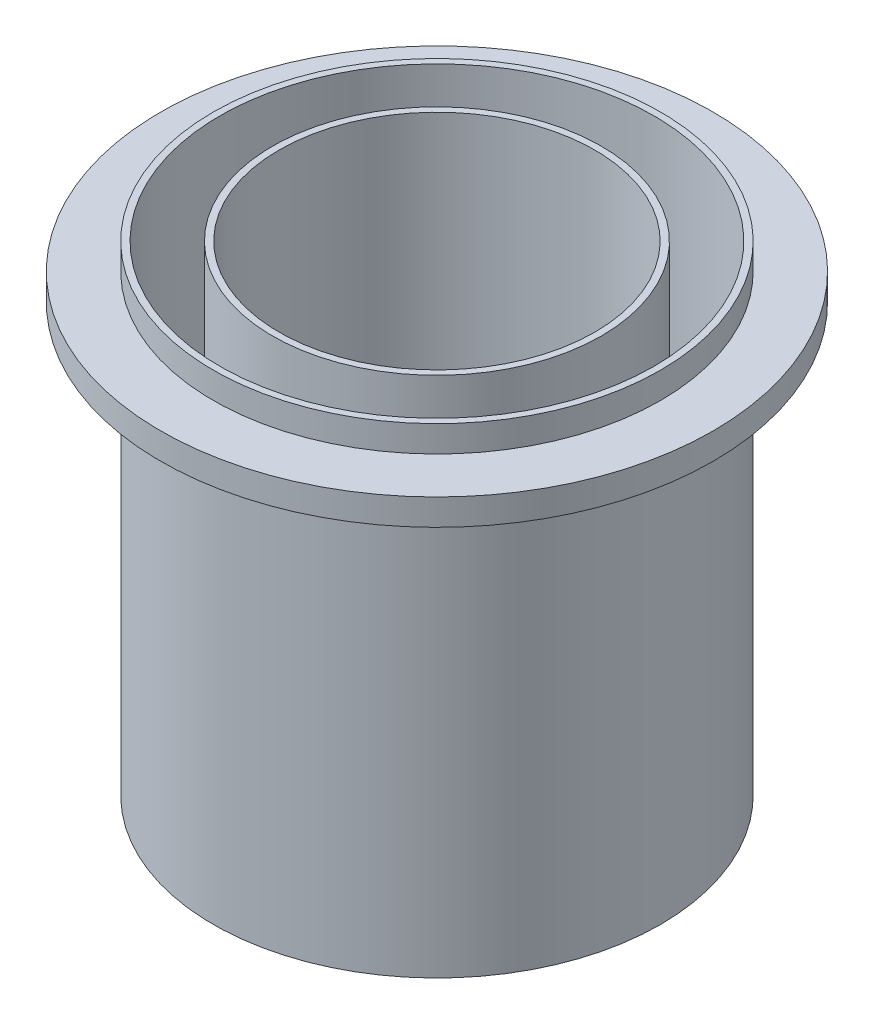
SolidWorks part; units mm, degrees
material "Delrin 2700 NC010, Low Viscosity Acetal Copolymer (SS)"
ref_plane "Front Plane" through (0, 0, 0) normal (0, 0, 1) x (1, 0, 0)
ref_plane "Top Plane" through (0, 0, 0) normal (0, 1, 0) x (1, 0, 0)
ref_plane "Right Plane" through (0, 0, 0) normal (1, 0, 0) x (0, 0, -1)
sketch "Sketch1" plane through (0, 0, 0) normal (0, 0, 1) x (1, 0, 0)
  line L0 (0, -554.3926) -> (0, 27165.2366) construction
  line L1 (53.975, 0) -> (30.744, 0)
  line L2 (53.975, 0) -> (53.975, 103.1875)
  line L3 (53.975, 115.8875) -> (52.3875, 115.8875)
  line L4 (52.3875, 115.8875) -> (52.3875, 1.5875)
  line L5 (52.3875, 1.5875) -> (39.6875, 1.5875)
  line L6 (53.975, 109.5375) -> (53.975, 115.8875)
  line L7 (39.6875, 1.5875) -> (39.6875, 115.8875)
  line L8 (39.6875, 115.8875) -> (38.1, 115.8875)
  line L9 (38.1, 115.8875) -> (38.1, 1.5875)
  line L10 (53.975, 109.5375) -> (66.675, 109.5375)
  line L11 (30.744, 0) -> (0, 0)
  line L12 (53.975, 103.1875) -> (66.675, 103.1875)
  line L13 (66.675, 109.5375) -> (66.675, 103.1875)
  line L14 (0, 0) -> (0, 1.5875)
  line L15 (0, 1.5875) -> (38.1, 1.5875)
  dimension "D1" = 76.2
  dimension "D2" = 15.875
  dimension "D3" = 1.5875
  dimension "D4" = 12.7
  dimension "D5" = 1.5875
  dimension "D6" = 1.5875
  dimension "D7" = 101.6
  dimension "D8" = 6.35
  dimension "D9" = 12.7
revolve "Revolve1" add sketch "Sketch1" angle 360 about L0
sketch "Sketch2" plane through (0, 1.5875, 0) normal (0, 1, 0) x (1, 0, 0)
  circle A0 centre (0, 19.05) radius 3.175
  dimension "D1" = 6.35
  dimension "D2" = 19.05
extrude "Cut-Extrude1" cut sketch "Sketch2" against normal through all
pattern_circular "CirPattern1" count 6 over 360 about axis through (0, 0, 0) along (0, 1, 0) of "Cut-Extrude1"
